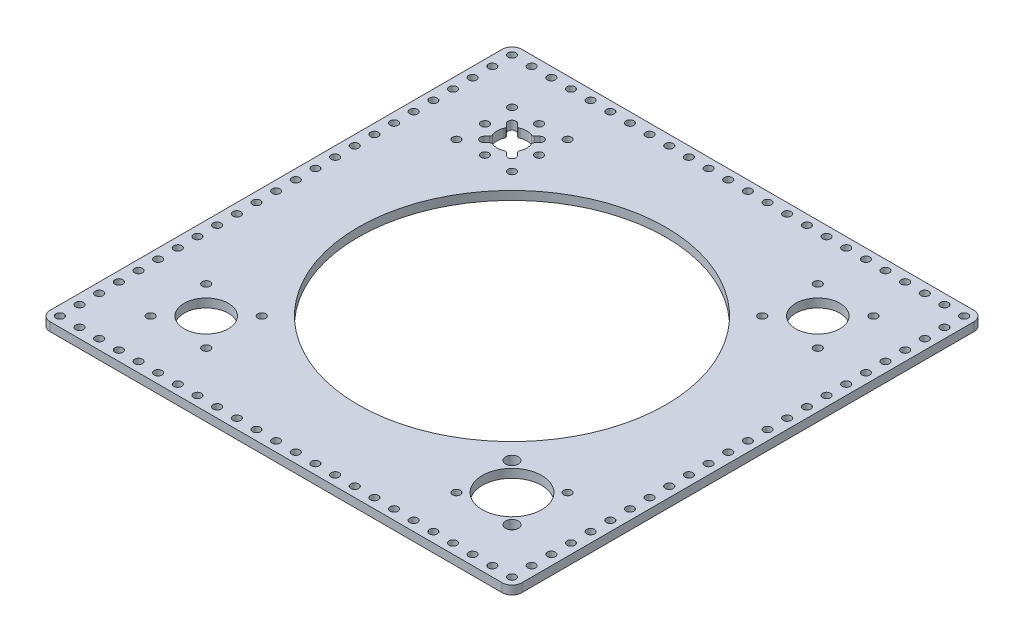
SolidWorks part; units mm, degrees
material "ABS PC"
ref_plane "Front Plane" through (0, 0, 0) normal (0, 0, 1) x (1, 0, 0)
ref_plane "Top Plane" through (0, 0, 0) normal (0, 1, 0) x (1, 0, 0)
ref_plane "Right Plane" through (0, 0, 0) normal (1, 0, 0) x (0, 0, -1)
ref_plane "Plane1" through (0, 0, 0) normal (0, -1, 0) x (1, 0, 0)
sketch "Sketch1" plane through (0, 0, 0) normal (0, -1, 0) x (1, 0, 0)
  line L0 (62.7626, -256.7181) -> (64.4025, -258.358)
  line L1 (60.7924, -261.9681) -> (59.1525, -260.3282)
  line L2 (48.0819, -260.3282) -> (46.442, -261.9681)
  line L3 (42.8319, -258.358) -> (44.4718, -256.7181)
  line L4 (44.4718, -245.6475) -> (42.8319, -244.0076)
  line L5 (46.442, -240.3975) -> (48.0819, -242.0374)
  line L6 (59.1525, -242.0374) -> (60.7924, -240.3975)
  line L7 (64.4025, -244.0076) -> (62.7626, -245.6475)
  line L8 (0, -6.35) -> (0, -298.45)
  line L9 (6.35, -304.8) -> (298.45, -304.8)
  line L10 (304.8, -298.45) -> (304.8, -6.35)
  line L11 (298.45, 0) -> (6.35, 0)
  arc A0 (62.4266, -247.3968) -> (62.4266, -254.9688) centre (53.6172, -251.1828) cw
  arc A1 (62.4266, -254.9688) -> (62.7626, -256.7181) centre (63.8851, -255.5956) ccw
  arc A2 (64.4025, -258.358) -> (60.7924, -261.9681) centre (62.5974, -260.1631) cw
  arc A3 (59.1525, -260.3282) -> (57.4032, -259.9922) centre (58.03, -261.4507) ccw
  arc A4 (57.4032, -259.9922) -> (49.8312, -259.9922) centre (53.6172, -251.1828) cw
  arc A5 (49.8312, -259.9922) -> (48.0819, -260.3282) centre (49.2044, -261.4507) ccw
  arc A6 (46.442, -261.9681) -> (42.8319, -258.358) centre (44.6369, -260.1631) cw
  arc A7 (44.4718, -256.7181) -> (44.8078, -254.9688) centre (43.3493, -255.5956) ccw
  arc A8 (44.8078, -254.9688) -> (44.8078, -247.3968) centre (53.6172, -251.1828) cw
  arc A9 (44.8078, -247.3968) -> (44.4718, -245.6475) centre (43.3493, -246.77) ccw
  arc A10 (42.8319, -244.0076) -> (46.442, -240.3975) centre (44.6369, -242.2026) cw
  arc A11 (48.0819, -242.0374) -> (49.8312, -242.3734) centre (49.2044, -240.9149) ccw
  arc A12 (49.8312, -242.3734) -> (57.4032, -242.3734) centre (53.6172, -251.1828) cw
  arc A13 (57.4032, -242.3734) -> (59.1525, -242.0374) centre (58.03, -240.9149) ccw
  arc A14 (60.7924, -240.3975) -> (64.4025, -244.0076) centre (62.5974, -242.2026) cw
  arc A15 (62.7626, -245.6475) -> (62.4266, -247.3968) centre (63.8851, -246.77) ccw
  circle A16 centre (152.4, -152.4) radius 99.375
  circle A17 centre (6.35, -298.45) radius 2.5527
  circle A18 centre (19.05, -298.45) radius 2.5527
  circle A19 centre (31.75, -298.45) radius 2.5527
  circle A20 centre (44.45, -298.45) radius 2.5527
  circle A21 centre (57.15, -298.45) radius 2.5527
  circle A22 centre (69.85, -298.45) radius 2.5527
  circle A23 centre (82.55, -298.45) radius 2.5527
  circle A24 centre (95.25, -298.45) radius 2.5527
  circle A25 centre (107.95, -298.45) radius 2.5527
  circle A26 centre (120.65, -298.45) radius 2.5527
  circle A27 centre (133.35, -298.45) radius 2.5527
  circle A28 centre (146.05, -298.45) radius 2.5527
  circle A29 centre (158.75, -298.45) radius 2.5527
  circle A30 centre (171.45, -298.45) radius 2.5527
  circle A31 centre (184.15, -298.45) radius 2.5527
  circle A32 centre (196.85, -298.45) radius 2.5527
  circle A33 centre (209.55, -298.45) radius 2.5527
  circle A34 centre (222.25, -298.45) radius 2.5527
  circle A35 centre (234.95, -298.45) radius 2.5527
  circle A36 centre (247.65, -298.45) radius 2.5527
  circle A37 centre (260.35, -298.45) radius 2.5527
  circle A38 centre (273.05, -298.45) radius 2.5527
  circle A39 centre (285.75, -298.45) radius 2.5527
  circle A40 centre (298.45, -298.45) radius 2.5527
  circle A41 centre (6.35, -6.35) radius 2.5527
  circle A42 centre (19.05, -6.35) radius 2.5527
  circle A43 centre (31.75, -6.35) radius 2.5527
  circle A44 centre (44.45, -6.35) radius 2.5527
  circle A45 centre (57.15, -6.35) radius 2.5527
  circle A46 centre (69.85, -6.35) radius 2.5527
  circle A47 centre (82.55, -6.35) radius 2.5527
  circle A48 centre (95.25, -6.35) radius 2.5527
  circle A49 centre (107.95, -6.35) radius 2.5527
  circle A50 centre (120.65, -6.35) radius 2.5527
  circle A51 centre (133.35, -6.35) radius 2.5527
  circle A52 centre (146.05, -6.35) radius 2.5527
  circle A53 centre (158.75, -6.35) radius 2.5527
  circle A54 centre (171.45, -6.35) radius 2.5527
  circle A55 centre (184.15, -6.35) radius 2.5527
  circle A56 centre (196.85, -6.35) radius 2.5527
  circle A57 centre (209.55, -6.35) radius 2.5527
  circle A58 centre (222.25, -6.35) radius 2.5527
  circle A59 centre (234.95, -6.35) radius 2.5527
  circle A60 centre (247.65, -6.35) radius 2.5527
  circle A61 centre (260.35, -6.35) radius 2.5527
  circle A62 centre (273.05, -6.35) radius 2.5527
  circle A63 centre (285.75, -6.35) radius 2.5527
  circle A64 centre (298.45, -6.35) radius 2.5527
  circle A65 centre (6.35, -285.75) radius 2.5527
  circle A66 centre (298.45, -285.75) radius 2.5527
  circle A67 centre (6.35, -273.05) radius 2.5527
  circle A68 centre (298.45, -273.05) radius 2.5527
  circle A69 centre (6.35, -260.35) radius 2.5527
  circle A70 centre (298.45, -260.35) radius 2.5527
  circle A71 centre (6.35, -247.65) radius 2.5527
  circle A72 centre (298.45, -247.65) radius 2.5527
  circle A73 centre (6.35, -234.95) radius 2.5527
  circle A74 centre (298.45, -234.95) radius 2.5527
  circle A75 centre (6.35, -222.25) radius 2.5527
  circle A76 centre (298.45, -222.25) radius 2.5527
  circle A77 centre (6.35, -209.55) radius 2.5527
  circle A78 centre (298.45, -209.55) radius 2.5527
  circle A79 centre (6.35, -196.85) radius 2.5527
  circle A80 centre (298.45, -196.85) radius 2.5527
  circle A81 centre (6.35, -184.15) radius 2.5527
  circle A82 centre (298.45, -184.15) radius 2.5527
  circle A83 centre (6.35, -171.45) radius 2.5527
  circle A84 centre (298.45, -171.45) radius 2.5527
  circle A85 centre (6.35, -158.75) radius 2.5527
  circle A86 centre (298.45, -158.75) radius 2.5527
  circle A87 centre (6.35, -146.05) radius 2.5527
  circle A88 centre (298.45, -146.05) radius 2.5527
  circle A89 centre (6.35, -133.35) radius 2.5527
  circle A90 centre (298.45, -133.35) radius 2.5527
  circle A91 centre (6.35, -120.65) radius 2.5527
  circle A92 centre (298.45, -120.65) radius 2.5527
  circle A93 centre (6.35, -107.95) radius 2.5527
  circle A94 centre (298.45, -107.95) radius 2.5527
  circle A95 centre (6.35, -95.25) radius 2.5527
  circle A96 centre (298.45, -95.25) radius 2.5527
  circle A97 centre (6.35, -82.55) radius 2.5527
  circle A98 centre (298.45, -82.55) radius 2.5527
  circle A99 centre (6.35, -69.85) radius 2.5527
  circle A100 centre (298.45, -69.85) radius 2.5527
  circle A101 centre (6.35, -57.15) radius 2.5527
  circle A102 centre (298.45, -57.15) radius 2.5527
  circle A103 centre (6.35, -44.45) radius 2.5527
  circle A104 centre (298.45, -44.45) radius 2.5527
  circle A105 centre (6.35, -31.75) radius 2.5527
  circle A106 centre (298.45, -31.75) radius 2.5527
  circle A107 centre (6.35, -19.05) radius 2.5527
  circle A108 centre (298.45, -19.05) radius 2.5527
  circle A109 centre (35.6567, -35.6567) radius 2.5527
  circle A110 centre (71.5777, -35.6567) radius 2.5527
  circle A111 centre (71.5777, -71.5777) radius 2.5527
  circle A112 centre (269.1433, -71.5777) radius 2.5527
  circle A113 centre (233.2223, -35.6567) radius 2.5527
  circle A114 centre (269.1433, -233.2223) radius 2.5527
  circle A115 centre (269.1433, -269.1433) radius 2.5527
  circle A116 centre (233.2223, -269.1433) radius 2.5527
  circle A117 centre (35.6567, -269.1433) radius 2.5527
  circle A118 centre (35.6567, -71.5777) radius 2.5527
  circle A119 centre (233.2223, -233.2223) radius 2.5527
  circle A120 centre (35.6567, -233.2223) radius 2.5527
  circle A121 centre (71.5777, -233.2223) radius 2.5527
  circle A122 centre (71.5777, -269.1433) radius 2.5527
  circle A123 centre (251.1828, -53.6172) radius 19.177
  circle A124 centre (233.2223, -71.5777) radius 4.1275
  circle A125 centre (269.1433, -35.6567) radius 4.1275
  circle A126 centre (251.1828, -251.1828) radius 14.2811
  circle A127 centre (53.6172, -53.6172) radius 14.2812
  circle A128 centre (53.6172, -268.6453) radius 2.5527
  circle A129 centre (71.0797, -251.1828) radius 2.5527
  circle A130 centre (53.6172, -233.7203) radius 2.5527
  circle A131 centre (36.1547, -251.1828) radius 2.5527
  arc A132 (0, -298.45) -> (6.35, -304.8) centre (6.35, -298.45) ccw
  arc A133 (298.45, -304.8) -> (304.8, -298.45) centre (298.45, -298.45) ccw
  arc A134 (304.8, -6.35) -> (298.45, 0) centre (298.45, -6.35) ccw
  arc A135 (6.35, 0) -> (0, -6.35) centre (6.35, -6.35) ccw
extrude "AndyMark Base" add sketch "Sketch1" against normal blind 5.588
chamfer "V Groove" [suppressed] distance 2.794 angle 45
